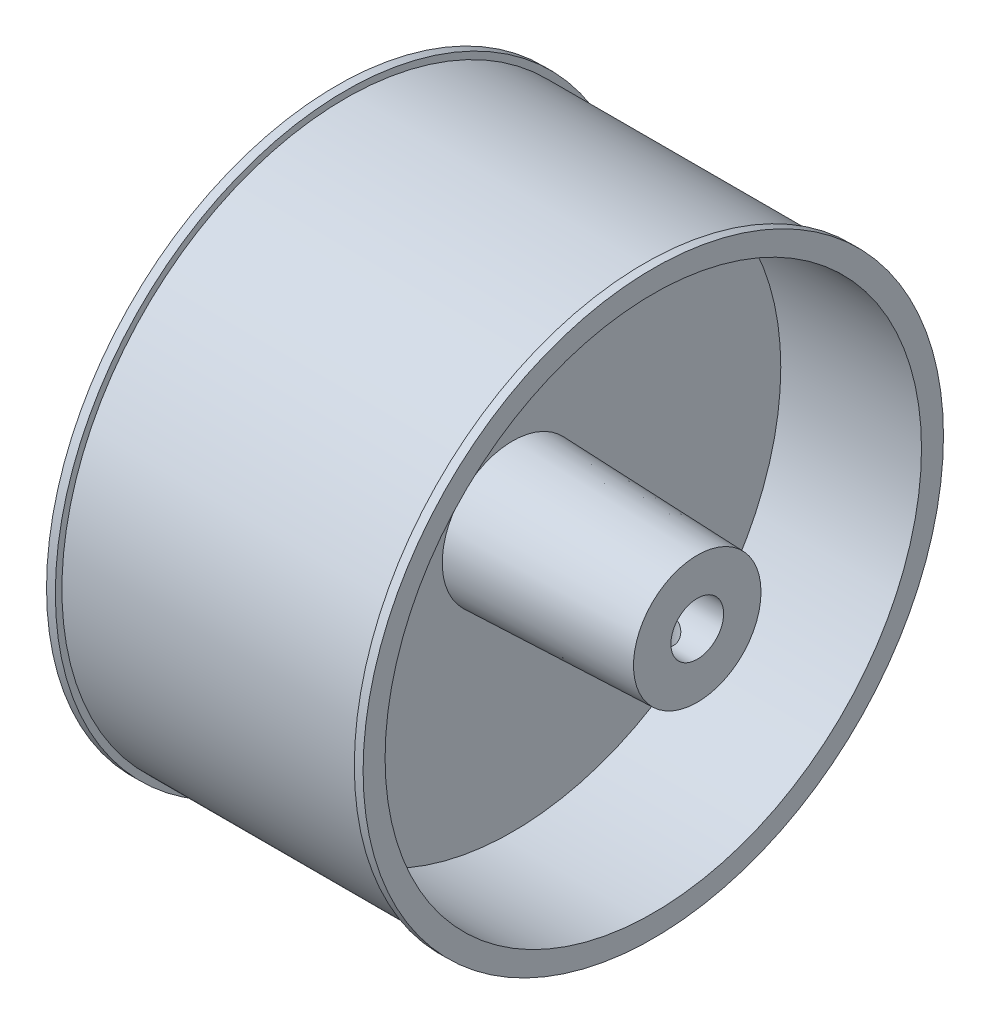
SolidWorks part; units mm, degrees
material "ABS"
ref_plane "Front Plane" through (0, 0, 0) normal (0, 0, 1) x (1, 0, 0)
ref_plane "Top Plane" through (0, 0, 0) normal (0, 1, 0) x (1, 0, 0)
ref_plane "Right Plane" through (0, 0, 0) normal (1, 0, 0) x (0, 0, -1)
sketch "Sketch1" plane through (0, 0, 0) normal (1, 0, 0) x (0, 0, -1)
  circle A0 centre (0, 0) radius 33
  dimension "D1" = 66
extrude "Boss-Extrude1" add sketch "Sketch1" along normal blind 36
sketch "Sketch2" plane through (36, 0, 0) normal (1, 0, 0) x (0, 0, -1)
  circle A0 centre (0, 0) radius 30.5
  circle A1 centre (0, 0) radius 8
  circle A2 centre (0, 0) radius 3
  dimension "D1" = 61
  dimension "D2" = 16
  dimension "D3" = 6
extrude "Cut-Extrude2" cut sketch "Sketch2" against normal blind 16 contours A2 | A1 A2 | A0 A1
sketch "Sketch5" plane through (20, 0, 0) normal (1, 0, 0) x (0, 0, -1)
  circle A0 centre (0, 0) radius 8
  dimension "D1" = 16
ref_plane "Plane1" through (41, 0, 0) normal (1, 0, 0) x (0, 0, -1)
sketch "Sketch6" plane through (41, 0, 0) normal (1, 0, 0) x (0, 0, -1)
  circle A0 centre (0, 0) radius 7.25
  dimension "D1" = 14.5
loft "Loft2" add profiles "Sketch6", "Sketch5"
sketch "Sketch7" plane through (0, 0, 0) normal (-1, 0, 0) x (0, 0, 1)
  circle A0 centre (0, 0) radius 30.5
  dimension "D1" = 61
extrude "Cut-Extrude3" cut sketch "Sketch7" against normal blind 18 contours A0
sketch "Sketch8" plane through (41, 0, 0) normal (1, 0, 0) x (0, 0, -1)
  circle A0 centre (0, 0) radius 3
  dimension "D1" = 6
extrude "Cut-Extrude4" cut sketch "Sketch8" against normal blind 77
ref_plane "Plane2" through (18, 0, 0) normal (1, 0, 0) x (0, 0, -1)
sketch "Sketch9" plane through (18, 0, 0) normal (1, 0, 0) x (0, 0, -1)
  circle A0 centre (0, 0) radius 32.25
  circle A1 centre (0, 0) radius 42.9059
  dimension "D1" = 64.5
extrude "Cut-Extrude5" cut sketch "Sketch9" against normal blind 17 and the other way blind 17
sketch "Sketch10" plane through (0, 0, 0) normal (0, 1, 0) x (1, 0, 0)
  circle A0 centre (36.3002, 0) radius 2
  dimension "D1" = 4
extrude "Cut-Extrude6" cut sketch "Sketch10" against normal blind 17
